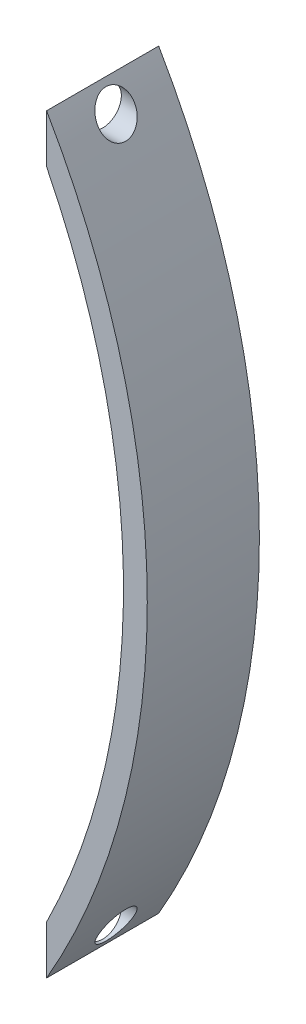
SolidWorks part; units mm, degrees
ref_plane "Front Plane" through (0, 0, 0) normal (0, 0, 1) x (1, 0, 0)
ref_plane "Top Plane" through (0, 0, 0) normal (0, 1, 0) x (1, 0, 0)
ref_plane "Right Plane" through (0, 0, 0) normal (1, 0, 0) x (0, 0, -1)
sketch "Sketch1" plane through (0, 0, 0) normal (0, 0, 1) x (1, 0, 0)
  line L12 (0, 0) -> (0, 6.5)
  line L13 (0, 94) -> (0, 100.5)
  arc A0 (0, 6.5) -> (0, 94) centre (-87.9133, 50.25) ccw
  arc A1 (0, 100.5) -> (0, 0) centre (-86.9981, 50.25) cw
  dimension "D3" = 98.1978
  dimension "D4" = 100.4675
  dimension "D1" = 6.5
  dimension "D2" = 6.5
  dimension "D5" = 87.5
extrude "Boss-Extrude1" add sketch "Sketch1" along normal blind 15
sketch "Sketch2" plane through (0, 0, 0) normal (-1, 0, 0) x (0, 0, 1)
  line L1 (0, 6.5) -> (0, 0) construction
  line L2 (7.5, 3.25) -> (0, 3.25) construction
  line L3 (7.5, 3.25) -> (7.5, 0) construction
  line L4 (15, 0) -> (0, 0) construction
  line L5 (7.5, 100.5) -> (7.5, 97.25) construction
  line L6 (15, 100.5) -> (0, 100.5) construction
  line L7 (7.5, 97.25) -> (0, 97.25) construction
  line L8 (0, 100.5) -> (0, 94) construction
  circle A0 centre (7.5, 97.25) radius 2.5
  circle A1 centre (7.5, 3.25) radius 2.5
  dimension "D1" = 5
  dimension "D2" = 5
extrude "Cut-Extrude1" cut sketch "Sketch2" against normal up to next
